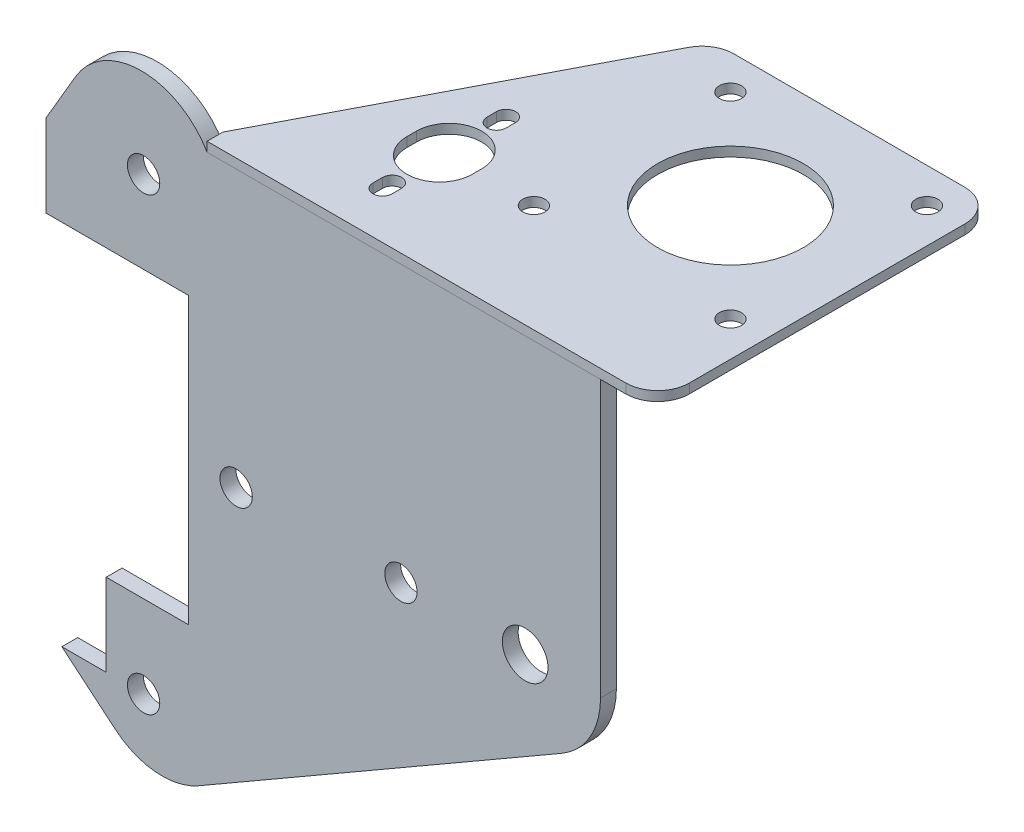
SolidWorks part; units mm, degrees
ref_plane "Front Plane" through (0, 0, 0) normal (0, 0, 1) x (1, 0, 0)
ref_plane "Top Plane" through (0, 0, 0) normal (0, 1, 0) x (1, 0, 0)
ref_plane "Right Plane" through (0, 0, 0) normal (1, 0, 0) x (0, 0, -1)
sketch "Sketch1" plane through (0, 0, 0) normal (0, 0, 1) x (1, 0, 0)
  line L0 (-75.2054, 35.5) -> (-70.514, 43.53)
  line L1 (-49.7915, 43.53) -> (12.2946, 43.53)
  line L4 (12.2946, 43.53) -> (12.2946, 0)
  line L5 (6.1473, -10.6474) -> (-51.1369, -43.7204)
  line L6 (-64.2789, -42.5707) -> (-72.7054, -35.5)
  line L7 (-72.7054, -35.5) -> (-65.7054, -35.5)
  line L8 (-65.7054, -35.5) -> (-65.7054, -22.5)
  line L9 (-65.7054, -22.5) -> (-52.7054, -22.5)
  line L10 (-52.7054, -22.5) -> (-52.7054, 22.5)
  line L11 (-52.7054, 22.5) -> (-75.2054, 22.5)
  line L12 (-75.2054, 22.5) -> (-75.2054, 35.5)
  arc A0 (-70.514, 43.53) -> (-49.7915, 43.53) centre (-60.1527, 37.4766) cw
  arc A1 (12.2946, 0) -> (6.1473, -10.6474) centre (0, 0) cw
  arc A2 (-51.1369, -43.7204) -> (-64.2789, -42.5707) centre (-56.8869, -33.7612) cw
  circle A3 centre (-59.8054, 35.5) radius 2.55
  circle A7 centre (-59.8054, -35.52) radius 2.55
  circle A8 centre (-45.2054, 0) radius 2.55
  circle A9 centre (-19.2054, 0) radius 2.55
  circle A10 centre (0.3946, 0) radius 3.6
  dimension "D1" = 87.5
  dimension "D8" = 11.5
  dimension "D9" = 12
  dimension "D16" = 8.03
  dimension "D18" = 5.1
  dimension "D19" = 79.05
  dimension "D21" = 31.5
  dimension "D20" = 11.9
  dimension "D23" = 7.2
  dimension "D2" = 65
  dimension "D3" = 21.03
  dimension "D4" = 66.03
  dimension "D5" = 79.03
  dimension "D6" = 43.53
  dimension "D7" = 120
  dimension "D10" = 9.3
  dimension "D11" = 13
  dimension "D12" = 13
  dimension "D13" = 7
  dimension "D14" = 11
  dimension "D15" = 40
  dimension "D17" = 72.1
  dimension "D22" = 57.5
extrude "Boss-Extrude1" add sketch "Sketch1" along normal blind 2.5
sketch "Sketch3" plane through (0, 43.53, 0) normal (0, 1, 0) x (1, 0, 0)
  line L0 (12.2946, 51) -> (12.2946, -2.5) construction
  line L1 (-49.7915, -2.5) -> (21.2946, -2.5)
  line L2 (-49.7915, -2.5) -> (-49.7915, 0)
  line L3 (-23.2312, 51) -> (21.2946, 51)
  line L4 (21.2946, -2.5) -> (21.2946, 51)
  line L5 (-49.7915, 0) -> (-23.2312, 51)
  line L6 (12.2946, 0) -> (-49.7915, 0) construction
  line L7 (-29.5054, 15.4) -> (-29.5054, 13.9) construction
  line L8 (-24.3554, 15.4) -> (-24.3554, 13.9)
  line L9 (-34.6554, 15.4) -> (-34.6554, 13.9)
  line L10 (-29.5054, 24.4) -> (-29.5054, 22.9) construction
  line L11 (-28.0054, 24.4) -> (-28.0054, 22.9)
  line L12 (-31.0054, 24.4) -> (-31.0054, 22.9)
  line L13 (-29.5054, 6.4) -> (-29.5054, 4.9) construction
  line L14 (-28.0054, 6.4) -> (-28.0054, 4.9)
  line L15 (-31.0054, 6.4) -> (-31.0054, 4.9)
  circle A0 centre (0.2946, 30) radius 11.5
  arc A1 (-24.3554, 15.4) -> (-34.6554, 15.4) centre (-29.5054, 15.4) ccw
  arc A2 (-34.6554, 13.9) -> (-24.3554, 13.9) centre (-29.5054, 13.9) ccw
  arc A3 (-28.0054, 24.4) -> (-31.0054, 24.4) centre (-29.5054, 24.4) ccw
  arc A4 (-31.0054, 22.9) -> (-28.0054, 22.9) centre (-29.5054, 22.9) ccw
  arc A5 (-28.0054, 6.4) -> (-31.0054, 6.4) centre (-29.5054, 6.4) ccw
  arc A6 (-31.0054, 4.9) -> (-28.0054, 4.9) centre (-29.5054, 4.9) ccw
  point P16 (-29.5054, 14.65)
  point P21 (-29.5054, 23.65)
  point P28 (-29.5054, 5.65)
  dimension "D4" = 32.5
  dimension "D17" = 23
  dimension "D2" = 53.5
  dimension "D3" = 62.49
  dimension "D5" = 21
  dimension "D6" = 10.3
  dimension "D7" = 1.5
  dimension "D8" = 17.15
  dimension "D9" = 26.15
  dimension "D10" = 1.5
  dimension "D11" = 8.15
  dimension "D12" = 3
  dimension "D13" = 3
  dimension "D14" = 50.8
  dimension "D15" = 44.5258
  dimension "D16" = 9
extrude "Boss-Extrude2" add sketch "Sketch3" along normal blind 1.5 separate body
sketch "Sketch5" plane through (0, 45.03, 0) normal (0, 1, 0) x (1, 0, 0)
  line L0 (21.2946, -2.5) -> (21.2946, 51) construction
  line L1 (21.2946, 51) -> (21.2946, -2.5) construction
  line L2 (-49.7915, -2.5) -> (21.2946, -2.5) construction
  circle A0 centre (-15.2154, 45.5) radius 1.75
  circle A1 centre (-15.2154, 14.4941) radius 1.75
  circle A2 centre (15.7946, 45.5) radius 1.75
  circle A3 centre (15.7946, 14.4941) radius 1.75
  point P4 (0, 0)
  point P5 (0, 0)
  point P8 (0, 0)
  point P11 (-16.3486, 14.4941)
  point P14 (-16.3617, 45.5)
  point P15 (-16.4368, 14.4941)
  point P16 (-15.2154, 14.4941)
  dimension "D1" = 5.5
  dimension "D2" = 48
  dimension "D3" = 31.0059
  dimension "D5" = 31.01
extrude "Cut-Extrude1" cut sketch "Sketch5" against normal through all
fillet "Fillet1" radius 5 3 edges at (21.2946, 44.28, 2.5) (21.2946, 44.28, -51) (-23.2312, 44.28, -51)
